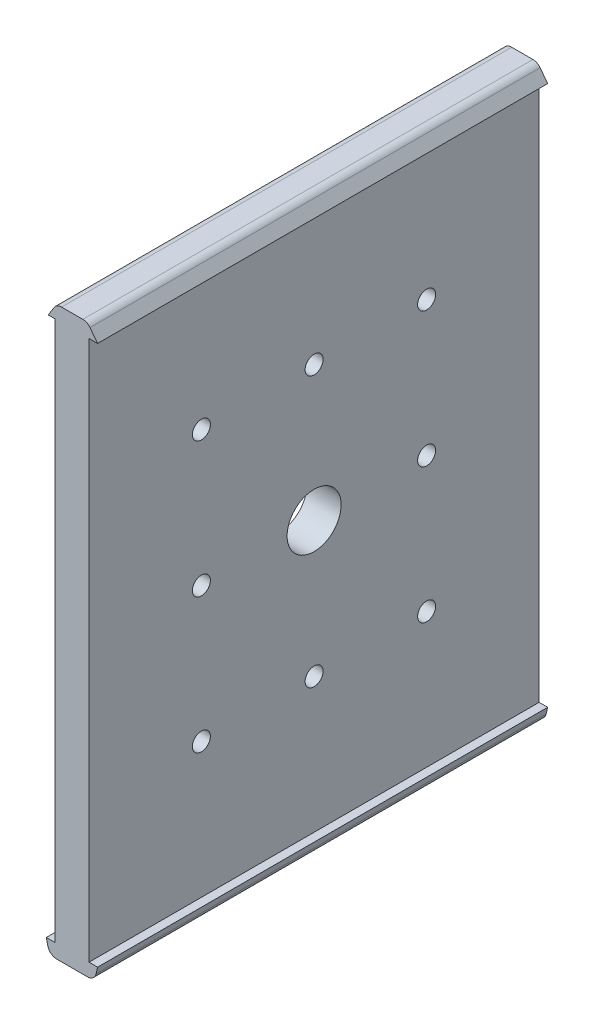
SolidWorks part; units mm, degrees
ref_plane "Plano frontal" through (0, 0, 0) normal (0, 0, 1) x (1, 0, 0)
ref_plane "Plano superior" through (0, 0, 0) normal (0, 1, 0) x (1, 0, 0)
ref_plane "Plano direito" through (0, 0, 0) normal (1, 0, 0) x (0, 0, -1)
sketch "Esboço1" plane through (0, 0, 0) normal (0, 0, 1) x (1, 0, 0)
  line L0 (0, 0) -> (0, 14.1176) construction
  line L1 (-3.8, -98.1786) -> (-5.7, -98.1786)
  line L2 (0, -101.1786) -> (0, -98.1786) construction
  line L3 (0, -98.1786) -> (-3.8, -98.1786) construction
  line L4 (-3.4129, -101.1786) -> (3.4129, -101.1786)
  line L5 (3.8, -98.1786) -> (0, -98.1786) construction
  line L6 (5.7, -98.1786) -> (5.7, -30.5351) construction
  line L7 (-5.3606, -99.6331) -> (-5.7, -98.1786)
  line L8 (5.7, -98.1786) -> (5.3606, -99.6331)
  line L9 (5.7, -30.5351) -> (5.7, 21.8214) construction
  line L10 (5.7, 21.8214) -> (3.4129, 21.8214) construction
  line L11 (3.8, -98.1786) -> (3.8, 21.8214)
  line L12 (3.8, 21.8214) -> (3.4129, 21.8214)
  line L13 (-3.8, -98.1786) -> (-3.8, 21.8214)
  line L14 (3.8, -98.1786) -> (5.7, -98.1786)
  line L15 (-5.2668, 21.8214) -> (-5.2668, 17.6583) construction
  line L16 (3.4129, -101.1786) -> (3.4129, 21.8214) construction
  line L17 (-3.4129, -101.1786) -> (-3.4129, 24.8214) construction
  line L18 (5.7, 21.8214) -> (3.4129, 21.8214)
  line L19 (3.4129, 21.8214) -> (3.4129, 24.8214) construction
  line L20 (5.7, 21.8214) -> (4.0133, 24.0339)
  line L21 (2.4227, 24.8214) -> (-2.2978, 24.8214)
  line L22 (-3.9992, 23.8727) -> (-5.2668, 21.8214)
  line L23 (-3.4129, 21.8214) -> (-5.2668, 21.8214) construction
  line L24 (-3.4129, 21.8214) -> (-3.8, 21.8214)
  line L25 (-3.4129, 21.8214) -> (-5.2668, 21.8214)
  arc A0 (3.4129, -101.1786) -> (5.3606, -99.6331) centre (3.4129, -99.1786) ccw
  arc A1 (-5.3606, -99.6331) -> (-3.4129, -101.1786) centre (-3.4129, -99.1786) ccw
  arc A2 (-2.2978, 24.8214) -> (-3.9992, 23.8727) centre (-2.2978, 22.8214) ccw
  arc A3 (2.4227, 24.8214) -> (4.0133, 24.0339) centre (2.4227, 22.8214) cw
  point P15 (5, -101.1786)
  point P18 (-5, -101.1786)
  dimension "D9" = 2
  dimension "D11" = 2
  dimension "D1" = 5.7
  dimension "D2" = 5.7
  dimension "D3" = 11.4
  dimension "D4" = 5.7
  dimension "D5" = 5
  dimension "D6" = 7.6
  dimension "D7" = 3.8
  dimension "D8" = 120
  dimension "D10" = 3
  dimension "D12" = 3
extrude "Ressalto-extrusão1" add sketch "Esboço1" along normal blind 160
sketch "Esboço2" plane through (0, 0, 0) normal (0, 0, 1) x (1, 0, 0)
  line L1 (-3.8, 21.8214) -> (3.8, 21.8214)
  line L2 (-3.8, 21.8214) -> (-3.8, -98.1786)
  line L3 (-3.8, -98.1786) -> (3.8, -98.1786)
  line L4 (3.8, 21.8214) -> (3.8, -98.1786)
extrude "Corte-extrusão1" cut sketch "Esboço2" along normal blind 30
sketch3d "3DSketch2"
  line L1 (-3.8, 21.8214, 160) -> (3.8, 21.8214, 160)
  line L2 (-3.8, 21.8214, 160) -> (-3.8, -98.1786, 160)
  line L3 (-3.8, -98.1786, 160) -> (3.8, -98.1786, 160)
  line L4 (3.8, 21.8214, 160) -> (3.8, -98.1786, 160)
  dimension "D1" = 160
extrude "Corte-extrusão2" cut sketch "3DSketch2" along direction (0, 0, 1) on the side of the normal blind 30
sketch3d "3DSketch3"
  line L0 (3.8, 21.8214, 130) -> (3.8, 21.8214, 80) construction
  line L1 (3.8, 21.8214, 130) -> (3.8, 21.8214, 30) construction
  line L2 (3.8, 21.8214, 80) -> (3.8, -98.1786, 80) construction
  line L3 (3.8, -98.1786, 130) -> (3.8, -98.1786, 30) construction
  line L4 (3.8, -98.1786, 80) -> (3.8, -98.1786, 130) construction
  line L5 (3.8, -98.1786, 130) -> (3.8, -38.1786, 130) construction
  line L6 (3.8, -98.1786, 130) -> (3.8, 21.8214, 130) construction
  line L7 (3.8, -38.1786, 130) -> (3.8, -38.1786, 30) construction
  line L8 (3.8, -98.1786, 30) -> (3.8, 21.8214, 30) construction
  line L9 (3.8, 21.8214, 130) -> (3.8, -98.1786, 30) construction
  line L10 (3.8, -98.1786, 30) -> (3.8, -98.1786, 130) construction
  line L11 (3.8, -98.1786, 130) -> (3.8, 21.8214, 30) construction
  line L12 (3.8, 21.8214, 30) -> (3.8, -38.1786, 130) construction
  line L13 (3.8, -38.1786, 130) -> (3.8, 21.8214, 130) construction
  line L14 (3.8, 21.8214, 130) -> (3.8, -38.1786, 30) construction
  line L15 (3.8, -38.1786, 30) -> (3.8, -8.1786, 30) construction
  line L16 (3.8, -8.1786, 30) -> (3.8, -8.1786, 130) construction
  line L17 (3.8, -38.1786, 130) -> (3.8, -98.1786, 30) construction
  line L18 (3.8, -98.1786, 30) -> (3.8, -98.1786, 130) construction
  line L19 (3.8, -98.1786, 130) -> (3.8, -38.1786, 30) construction
  line L20 (3.8, -68.1786, 80) -> (3.8, -68.1786, 30) construction
  line L21 (3.8, -68.1786, 30) -> (3.8, -68.1786, 130) construction
  line L22 (3.8, 21.8214, 105) -> (3.8, -98.1786, 80) construction
  line L23 (3.8, -98.1786, 80) -> (3.8, -98.1786, 105) construction
  line L24 (3.8, -98.1786, 105) -> (3.8, 21.8214, 80) construction
  line L25 (3.8, 21.8214, 80) -> (3.8, -98.1786, 55) construction
  line L26 (3.8, -98.1786, 55) -> (3.8, 21.8214, 55) construction
  line L27 (3.8, 21.8214, 55) -> (3.8, -98.1786, 80) construction
  line L28 (3.8, -98.1786, 80) -> (3.8, -38.1786, 67.5) construction
  line L29 (3.8, -38.1786, 67.5) -> (3.8, -98.1786, 67.5) construction
  line L30 (3.8, -98.1786, 67.5) -> (3.8, 21.8214, 67.5) construction
  line L31 (3.8, -38.1786, 92.5213) -> (3.8, 21.8214, 92.5213) construction
  line L32 (3.8, 21.8214, 92.5213) -> (3.8, -98.1786, 92.5213) construction
  circle A0 centre (3.8, -38.1786, 80) radius 2
  circle A1 centre (3.8, -8.1786, 80) radius 2
  circle A2 centre (3.8, -68.1786, 80) radius 2
  circle A3 centre (3.8, -68.1786, 55) radius 2
  circle A4 centre (3.8, -38.1786, 55) radius 2
  circle A5 centre (3.8, -8.1786, 55) radius 2
  circle A6 centre (3.8, -68.1786, 105.0426) radius 2
  circle A7 centre (3.8, -38.1786, 105.0426) radius 2
  circle A8 centre (3.8, -8.1786, 105.0426) radius 2
  point P18 (5.8, -38.1786, 80)
  point P27 (5.8, -8.1786, 80)
  point P32 (5.8, -68.1786, 80)
  point P42 (5.8, -68.1786, 55)
  point P45 (5.8, -38.1786, 55)
  point P48 (5.8, -8.1786, 55)
  point P54 (5.8, -68.1786, 105.0426)
  point P57 (5.8, -38.1786, 105.0426)
  point P60 (5.8, -8.1786, 105.0426)
extrude "Corte-extrusão3" cut sketch "3DSketch3" along direction (-1, 0, 0) on the side against the normal blind 70
sketch "Esboço3" plane through (0, 0, 0) normal (1, 0, 0) x (0, 0, -1)
  line L0 (-130, 21.8214) -> (-130, 24.8214) construction
  line L1 (-160, 24.8214) -> (0, 24.8214) construction
  line L2 (-130, 24.8214) -> (-30, 21.8214) construction
  line L3 (-30, 21.8214) -> (-30, 24.8214) construction
  line L4 (-30, -98.1786) -> (-30, -101.1786) construction
  line L5 (-160, -101.1786) -> (0, -101.1786) construction
  line L6 (-30, -101.1786) -> (-130, -98.1786) construction
  line L7 (-130, -98.1786) -> (-130, -101.1786) construction
  line L9 (-30, 24.8214) -> (15.0153, 24.8214)
  line L10 (-30, 24.8214) -> (-30, -104.6572)
  line L11 (-30, -104.6572) -> (15.0153, -104.6572)
  line L12 (15.0153, 24.8214) -> (15.0153, -104.6572)
  line L13 (-130, 24.8214) -> (-167.1926, 24.8214)
  line L14 (-130, 24.8214) -> (-130, -104.6572)
  line L15 (-130, -104.6572) -> (-167.1926, -104.6572)
  line L16 (-167.1926, 24.8214) -> (-167.1926, -104.6572)
  circle A2 centre (-80, -38.1786) radius 6
extrude "Corte-extrusão4" cut sketch "Esboço3" along normal blind 41 and the other way blind 22
